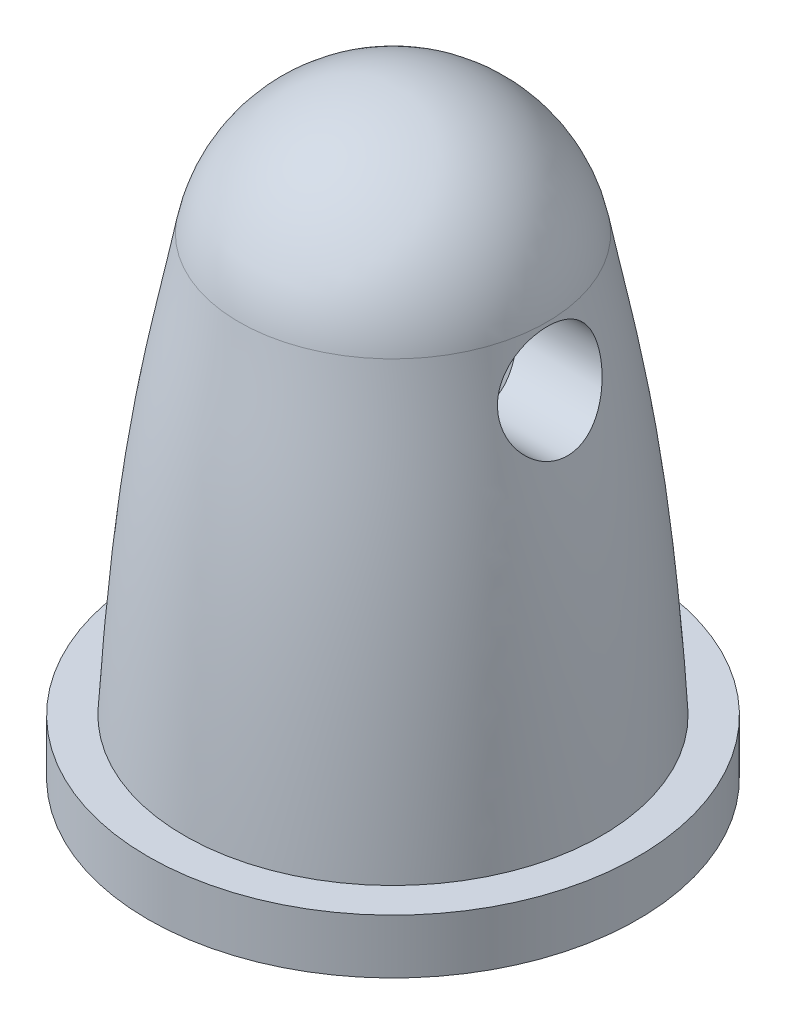
SolidWorks part; units mm, degrees
ref_plane "Front Plane" through (0, 0, 0) normal (0, 0, 1) x (1, 0, 0)
ref_plane "Top Plane" through (0, 0, 0) normal (0, 1, 0) x (1, 0, 0)
ref_plane "Right Plane" through (0, 0, 0) normal (1, 0, 0) x (0, 0, -1)
sketch "Sketch1" plane through (0, 0, 0) normal (0, 0, 1) x (1, 0, 0)
  line L0 (0, 0) -> (-5.75, 0)
  line L4 (0, 15) -> (0, 0)
  arc A0 (-4.2417, 11.5) -> (0, 15) centre (0, 10.6797) cw
  spline S0 degree 3 poles (-5.75, 0) (-5.3855, 6.4999) (-4.8014, 8.4982) (-4.2417, 11.5) knots 0 0 0 0 1 1 1 1
  dimension "D1" = 3.5
  dimension "D2" = 15
  dimension "D3" = 5.75
revolve "Revolve1" add sketch "Sketch1" angle 360 about L4
sketch "Sketch3" plane through (0, 0, 0) normal (0, -1, 0) x (1, 0, 0)
  circle A0 centre (0, 0) radius 6.75
  circle A2 centre (0, 0) radius 5.75 construction
  dimension "D1" = 1
extrude "Boss-Extrude1" add sketch "Sketch3" along normal blind 1.5
sketch "Sketch5" plane through (0, -1.5, 0) normal (0, -1, 0) x (1, 0, 0)
  circle A0 centre (0, 0) radius 2.5
  dimension "D1" = 5
extrude "Cut-Extrude1" cut sketch "Sketch5" against normal blind 11
sketch "Sketch6" plane through (0, 0, 0) normal (1, 0, 0) x (0, 0, -1)
  circle A0 centre (0, 10) radius 1.4081
  dimension "D1" = 10
extrude "Cut-Extrude2" cut sketch "Sketch6" against normal through all both and the other way through all
